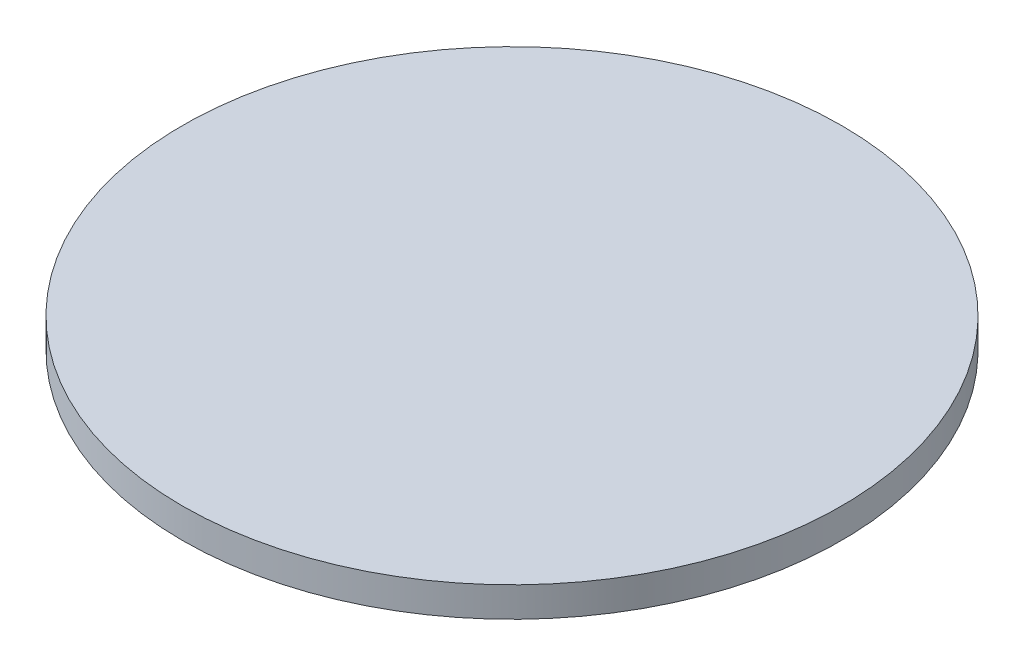
SolidWorks part; units mm, degrees
ref_plane "Front Plane" through (0, 0, 0) normal (0, 0, 1) x (1, 0, 0)
ref_plane "Top Plane" through (0, 0, 0) normal (0, 1, 0) x (1, 0, 0)
ref_plane "Right Plane" through (0, 0, 0) normal (1, 0, 0) x (0, 0, -1)
sketch "Sketch1" plane through (0, 0, 0) normal (0, 1, 0) x (1, 0, 0)
  circle A0 centre (0, 0) radius 35
extrude "Boss-Extrude3" add sketch "Sketch1" along normal blind 3.175
sketch "Sketch3" plane through (0, 3.175, 0) normal (0, 1, 0) x (1, 0, 0)
  line L0 (-30.362, 17.4112) -> (17.5779, 30.2658) construction
  circle A0 centre (0, 0) radius 35 construction
